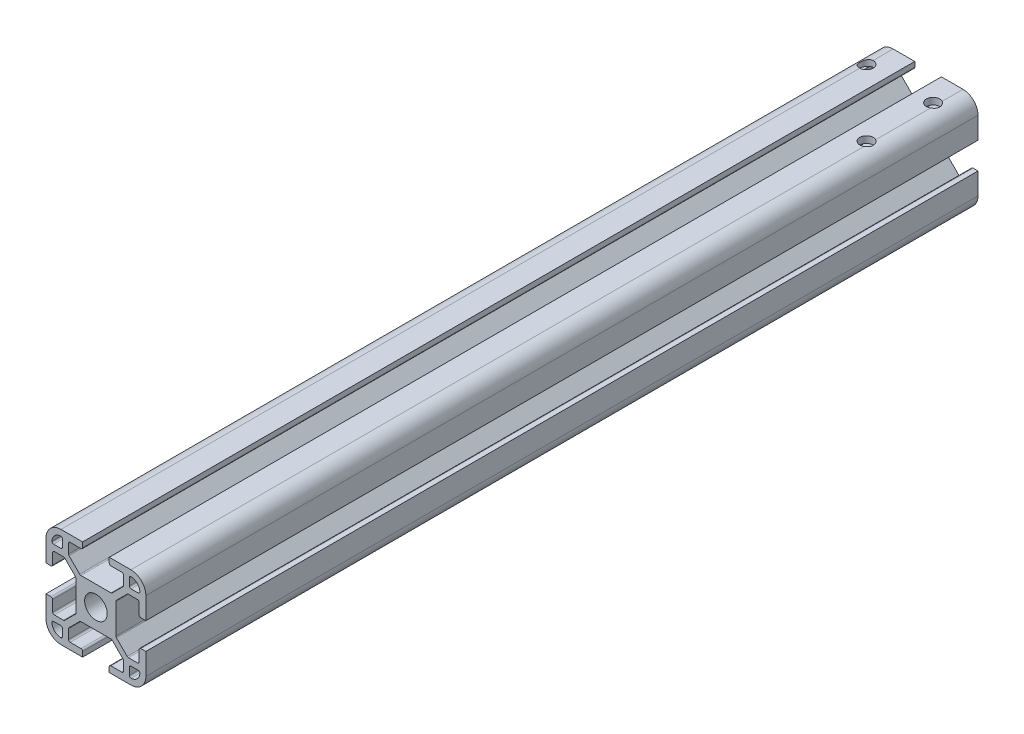
SolidWorks part; units mm, degrees
ref_plane "前基準面" through (0, 0, 0) normal (0, 0, 1) x (1, 0, 0)
ref_plane "上基準面" through (0, 0, 0) normal (0, 1, 0) x (1, 0, 0)
ref_plane "右基準面" through (0, 0, 0) normal (1, 0, 0) x (0, 0, -1)
sketch "草圖1" plane through (0, 0, 0) normal (0, 0, 1) x (1, 0, 0)
  line L0 (-15, 0) -> (0, 0) construction
  line L1 (-10.5, 15) -> (10.5, 15)
  line L2 (-15, 10.5) -> (-15, -10.5)
  line L3 (-10.5, -15) -> (10.5, -15)
  line L4 (15, 10.5) -> (15, -10.5)
  line L5 (0, 0) -> (0, 15) construction
  arc A0 (-10.5, 15) -> (-15, 10.5) centre (-10.5, 10.5) ccw
  arc A1 (-15, -10.5) -> (-10.5, -15) centre (-10.5, -10.5) ccw
  arc A2 (10.5, -15) -> (15, -10.5) centre (10.5, -10.5) ccw
  arc A3 (10.5, 15) -> (15, 10.5) centre (10.5, 10.5) cw
  circle A4 centre (0, 0) radius 3.4
  point P10 (-15, 15)
  point P17 (15, 15)
  dimension "D2" = 4.5
  dimension "D3" = 6.8
  dimension "MD1" = 30
extrude "填料-伸長1" add sketch "草圖1" against normal blind 250
sketch "草圖2" plane through (0, 0, 0) normal (0, 0, 1) x (1, 0, 0)
  line L0 (-8.25, 13) -> (-8.25, 9.5228)
  line L1 (-9.5228, 8.25) -> (-13, 8.25)
  line L2 (-8.25, 8.25) -> (-6, 6) construction
  line L3 (-9.5228, 8.25) -> (-6, 4.7272)
  line L4 (-8.25, 9.5228) -> (-4.7272, 6)
  line L5 (-7.6136, 8.8864) -> (-5.3636, 6.6364) construction
  line L6 (-8.8864, 7.6136) -> (-6.6364, 5.3636) construction
  line L7 (-8.25, 18.2) -> (-8.25, 8.25) construction
  line L8 (-8.25, 8.25) -> (-18.2, 8.25) construction
  line L9 (-4, 15) -> (-4, 13)
  line L10 (4, 15) -> (4, 13)
  line L12 (15, 4) -> (13, 4)
  line L13 (8.25, 13) -> (8.25, 9.5228)
  line L14 (9.5228, 8.25) -> (6, 4.7272)
  line L15 (8.25, 9.5228) -> (4.7272, 6)
  line L16 (-4, 13) -> (-8.25, 13)
  line L17 (4, 13) -> (8.25, 13)
  line L18 (-4, 15) -> (4, 15)
  line L19 (4.7272, 6) -> (-4.7272, 6)
  line L20 (0, 15) -> (0, 0) construction
  line L21 (10.5, 15) -> (-10.5, 15) construction
  line L22 (0, 0) -> (-15, 0) construction
  line L23 (-15, 10.5) -> (-15, -10.5) construction
  line L24 (13.2, -10.5) -> (13.2, 10.5)
  line L25 (-10.5, -13.2) -> (10.5, -13.2)
  line L26 (-13.2, 10.5) -> (-13.2, -10.5)
  line L27 (10.5, 13.2) -> (-10.5, 13.2)
  line L28 (13.2, -10.5) -> (13.2, 10.5) construction
  line L29 (-10.5, -13.2) -> (10.5, -13.2) construction
  line L30 (-13.2, 10.5) -> (-13.2, -10.5) construction
  line L31 (10.5, 13.2) -> (-10.5, 13.2) construction
  line L32 (-10.05, 13.2) -> (-10.05, 10.05)
  line L33 (-6, -6) -> (6, -6) construction
  line L34 (-6, -6) -> (-6, 6) construction
  line L35 (-6, 6) -> (6, 6) construction
  line L36 (6, -6) -> (6, 6) construction
  line L37 (-6, -6) -> (6, 6) construction
  line L38 (-6, 6) -> (6, -6) construction
  line L39 (10.05, 13.2) -> (10.05, 10.05)
  line L40 (-10.05, 10.05) -> (-13.2, 10.05)
  line L41 (10.05, 10.05) -> (13.2, 10.05)
  line L42 (10.05, -10.05) -> (13.2, -10.05)
  line L43 (10.05, -13.2) -> (10.05, -10.05)
  line L44 (-10.05, -10.05) -> (-13.2, -10.05)
  line L45 (-10.05, -13.2) -> (-10.05, -10.05)
  line L46 (-10.05, 13.2) -> (-10.5, 13.2)
  line L47 (-13.2, 10.5) -> (-13.2, 10.05)
  line L48 (-13.2, -10.5) -> (-13.2, -10.05)
  line L49 (-10.05, -13.2) -> (-10.5, -13.2)
  line L50 (10.05, -13.2) -> (10.5, -13.2)
  line L51 (13.2, -10.5) -> (13.2, -10.05)
  line L52 (13.2, 10.5) -> (13.2, 10.05)
  line L53 (10.05, 13.2) -> (10.5, 13.2)
  line L54 (-15, -4) -> (-15, 4)
  line L55 (-15, 4) -> (-13, 4)
  line L56 (-13, 4) -> (-13, 8.25)
  line L57 (-15, -4) -> (-13, -4)
  line L58 (-13, -4) -> (-13, -8.25)
  line L59 (-4, -15) -> (-4, -13)
  line L60 (-4, -13) -> (-8.25, -13)
  line L61 (-8.25, -13) -> (-8.25, -9.5228)
  line L62 (-8.25, -9.5228) -> (-4.7272, -6)
  line L63 (-9.5228, -8.25) -> (-6, -4.7272)
  line L64 (-9.5228, -8.25) -> (-13, -8.25)
  line L65 (-6, 4.7272) -> (-6, -4.7272)
  line L66 (13, 4) -> (13, 8.25)
  line L67 (9.5228, 8.25) -> (13, 8.25)
  line L68 (13, -4) -> (13, -8.25)
  line L69 (4, -15) -> (4, -13)
  line L70 (4, -13) -> (8.25, -13)
  line L71 (8.25, -13) -> (8.25, -9.5228)
  line L72 (8.25, -9.5228) -> (4.7272, -6)
  line L73 (9.5228, -8.25) -> (6, -4.7272)
  line L74 (9.5228, -8.25) -> (13, -8.25)
  line L75 (15, -4) -> (13, -4)
  line L76 (15, 4) -> (15, -4)
  line L77 (4, -15) -> (-4, -15)
  line L78 (-4.7272, -6) -> (4.7272, -6)
  line L79 (6, -4.7272) -> (6, 4.7272)
  line L80 (-10.05, 10.05) -> (-18.2, 10.05) construction
  line L81 (-10.05, 18.2) -> (-10.05, 10.05) construction
  arc A0 (10.5, -13.2) -> (13.2, -10.5) centre (10.5, -10.5) ccw
  arc A1 (10.5, 13.2) -> (13.2, 10.5) centre (10.5, 10.5) cw
  arc A16 (-10.5, 13.2) -> (-13.2, 10.5) centre (-10.5, 10.5) ccw
  arc A17 (-10.5, -13.2) -> (-13.2, -10.5) centre (-10.5, -10.5) cw
  arc A20 (13.2, 10.5) -> (10.5, 13.2) centre (10.5, 10.5) ccw
  arc A21 (10.5, -13.2) -> (13.2, -10.5) centre (10.5, -10.5) ccw
  arc A22 (-13.2, -10.5) -> (-10.5, -13.2) centre (-10.5, -10.5) ccw
  arc A23 (-10.5, 13.2) -> (-13.2, 10.5) centre (-10.5, 10.5) ccw
  arc A24 (13.2, 10.5) -> (10.5, 13.2) centre (10.5, 10.5) ccw construction
  arc A25 (10.5, -13.2) -> (13.2, -10.5) centre (10.5, -10.5) ccw construction
  arc A26 (-13.2, -10.5) -> (-10.5, -13.2) centre (-10.5, -10.5) ccw construction
  arc A27 (-10.5, 13.2) -> (-13.2, 10.5) centre (-10.5, 10.5) ccw construction
  point P86 (-10.05, -13.2)
  point P89 (-13.2, -10.05)
  point P92 (-10.05, -10.05)
  point P95 (-13, -4)
  point P98 (-6, -4.7272)
  point P101 (-13, -8.25)
  point P104 (-9.5228, -8.25)
  point P107 (-4, -13)
  point P110 (-8.25, -13)
  point P113 (-8.25, -9.5228)
  point P116 (-4.7272, -6)
  point P119 (4, -13)
  point P122 (8.25, -13)
  point P125 (10.05, -13.2)
  point P128 (13.2, -10.05)
  point P131 (10.05, -10.05)
  point P134 (8.25, -9.5228)
  point P137 (4.7272, -6)
  point P140 (13, -4)
  point P143 (13, -8.25)
  point P146 (9.5228, -8.25)
  point P149 (6, -4.7272)
  point P152 (6, 4.7272)
  point P155 (13, 4)
  point P158 (13, 8.25)
  point P161 (9.5228, 8.25)
  point P164 (13.2, 10.05)
  point P167 (10.05, 10.05)
  point P170 (10.05, 13.2)
  point P173 (-6, 4.7272)
  point P176 (-4.7272, 6)
  point P179 (4.7272, 6)
  point P182 (8.25, 9.5228)
  point P185 (8.25, 13)
  point P188 (4, 13)
  point P191 (-4, 13)
  point P194 (-8.25, 13)
  point P197 (-9.5228, 8.25)
  point P200 (-13, 4)
  point P203 (-13, 8.25)
  point P207 (-13.2, 10.05)
  dimension "D2" = 12
  dimension "MD8" = 8
  dimension "D9" = 7
  dimension "MD3" = 16.5
  dimension "MD4" = 16.5
  dimension "D1" = 1.8
  dimension "D5" = 1.8
  dimension "D6" = 0.9
  dimension "D7" = 0.9
extrude "除料-伸長1" cut sketch "草圖2" against normal up to next
fillet "圓角1" radius 0.5 44 edges at (-4, -13, -125) (4, -13, -125) (4, 13, -125) (9.5228, 8.25, -125) (13, 8.25, -125) (13, 4, -125) (13, -4, -125) (9.5228, -8.25, -125) (13, -8.25, -125) (8.25, -13, -125) (-8.25, -13, -125) (8.25, -9.5228, -125) (-8.25, -9.5228, -125) (-4.7272, -6, -125) (4.7272, -6, -125) (6, -4.7272, -125) (6, 4.7272, -125) (4.7272, 6, -125) (-6, 4.7272, -125) (-6, -4.7272, -125) (-9.5228, -8.25, -125) (-13, -8.25, -125) (-13, -4, -125) (-13, 4, -125) (-9.5228, 8.25, -125) (-13, 8.25, -125) (-4.7272, 6, -125) (-8.25, 9.5228, -125) (-4, 13, -125) (-8.25, 13, -125) (10.05, 13.2, -125) (10.05, 10.05, -125) (13.2, 10.05, -125) (-10.05, 13.2, -125) (-10.05, 10.05, -125) (-13.2, 10.05, -125) (-13.2, -10.05, -125) (-10.05, -13.2, -125) (10.05, -13.2, -125) (13.2, -10.05, -125) (10.05, -10.05, -125) (-10.05, -10.05, -125) (8.25, 9.5228, -125) (8.25, 13, -125)
sketch "草圖3" plane through (0, 0, 0) normal (0, 0, 1) x (1, 0, 0)
  line L0 (0, 21.6264) -> (0, 0) construction
  line L1 (-3.4, 0) -> (3.4, 0)
  line L2 (3.9, 0.5) -> (3.9, 0.8)
  line L3 (3.9, 0.8) -> (6.7235, 0.8)
  line L4 (7.1787, 1.5069) -> (5.1332, 6.0069)
  line L5 (4.678, 6.3) -> (-4.678, 6.3)
  line L6 (-7.1787, 1.5069) -> (-5.1332, 6.0069)
  line L7 (-3.9, 0.8) -> (-6.7235, 0.8)
  line L8 (-3.9, 0.5) -> (-3.9, 0.8)
  arc A0 (3.4, 0) -> (3.9, 0.5) centre (3.4, 0.5) ccw
  arc A1 (-3.9, 0.5) -> (-3.4, 0) centre (-3.4, 0.5) ccw
  arc A2 (-7.1787, 1.5069) -> (-6.7235, 0.8) centre (-6.7235, 1.3) ccw
  arc A3 (-5.1332, 6.0069) -> (-4.678, 6.3) centre (-4.678, 5.8) cw
  arc A4 (5.1332, 6.0069) -> (4.678, 6.3) centre (4.678, 5.8) ccw
  arc A5 (6.7235, 0.8) -> (7.1787, 1.5069) centre (6.7235, 1.3) ccw
  point P9 (0, 6.3)
  point P14 (3.9, 0)
  point P17 (-3.9, 0)
  point P20 (-7.5, 0.8)
  point P23 (-5, 6.3)
  point P26 (5, 6.3)
  point P29 (7.5, 0.8)
  dimension "D6" = 0.5
  dimension "D1" = 7.8
  dimension "D2" = 15
  dimension "D3" = 5.5
  dimension "D4" = 6.3
  dimension "D5" = 10
extrude "填料-伸長2" [suppressed] add sketch "草圖3" along normal mid plane 14
hole_wizard "M4 螺紋孔1" [suppressed] positions "草圖6" profile "草圖7" tap size "M4" standard "ISO"
sketch "草圖6" [suppressed] plane through (0.7411, 0, -5.4586) normal (0, 1, 0) x (-1, 0, 0)
  point P0 (0.7411, 5.4586)
sketch "草圖7" plane through (0, 0, 0) normal (1, 0, 0) x (0, 0, -1)
  line L0 (0, 0) -> (0, 6.3)
  line L1 (0, 6.3) -> (1.65, 6.3)
  line L2 (1.65, 6.3) -> (1.65, 0)
  line L5 (1.65, 0) -> (0, 0)
  line L11 (0, -6.35) -> (0, 107.95) construction
  dimension "貫穿螺孔鑽直徑" = 3.3
  dimension "貫穿螺孔鑽深度" = 6.3
cosmetic thread "鑽孔螺紋2" parameters "D2"=4
sketch "草圖8" plane through (0, 0, 0) normal (0, 0, 1) x (1, 0, 0)
  line L0 (-4, 30) -> (-30, 4)
  line L1 (0, 0) -> (-30, 0)
  line L2 (0, 0) -> (0, 30)
  line L3 (0, 30) -> (-4, 30)
  line L4 (-30, 0) -> (-30, 4)
  line L7 (-30, 4) -> (-4, 4) construction
  line L8 (-4, 30) -> (-4, 4) construction
  dimension "D1" = 30
  dimension "D2" = 30
  dimension "D3" = 4
  dimension "D4" = 4
extrude "填料-伸長3" [suppressed] add sketch "草圖8" along normal mid plane 20
shell "薄殼1" [suppressed] thickness 4
hole_wizard "M4 螺紋孔2" [suppressed] positions "草圖11" profile "草圖12" tap size "M4" standard "ISO"
sketch "草圖11" [suppressed] plane through (0, 4, 0) normal (0, 1, 0) x (-1, 0, 0)
  line L0 (17, 6) -> (17, 0) construction
  line L1 (30, 6) -> (4, 6) construction
  line L2 (17, 0) -> (30, 0) construction
  line L3 (30, 6) -> (30, -6) construction
  point P0 (17, 0)
sketch "草圖12" plane through (-17, 4, 0) normal (1, 0, 0) x (0, 0, 1)
  line L0 (0, 0) -> (0, 19)
  line L1 (0, 19) -> (1.65, 19)
  line L2 (1.65, 19) -> (1.65, 0)
  line L5 (1.65, 0) -> (0, 0)
  line L11 (0, -6.35) -> (0, 107.95) construction
  dimension "貫穿螺孔鑽直徑" = 3.3
  dimension "貫穿螺孔鑽深度" = 19
cosmetic thread "鑽孔螺紋3" parameters "D2"=4
hole_wizard "M4 螺紋孔3" [suppressed] positions "草圖13" profile "草圖14" tap size "M4" standard "ISO"
sketch "草圖13" [suppressed] plane through (-4, 0, 0) normal (-1, 0, 0) x (0, -1, 0)
  line L0 (-17, 6) -> (-17, 0) construction
  line L2 (-17, 0) -> (-4, 0) construction
  line L4 (-4, 6) -> (-30, 6) construction
  line L5 (-4, 6) -> (-4, -6) construction
  point P0 (-17, 0)
sketch "草圖14" plane through (-4, 17, 0) normal (0, 1, 0) x (0, 0, 1)
  line L0 (0, 0) -> (0, 19)
  line L1 (0, 19) -> (1.65, 19)
  line L2 (1.65, 19) -> (1.65, 0)
  line L5 (1.65, 0) -> (0, 0)
  line L11 (0, -6.35) -> (0, 107.95) construction
  dimension "貫穿螺孔鑽直徑" = 3.3
  dimension "貫穿螺孔鑽深度" = 4
cosmetic thread "鑽孔螺紋3" parameters "D2"=4
fillet "圓角2" [suppressed] radius 1
fillet "圓角3" [suppressed] radius 1
sketch "草圖15" plane through (0, 15, 0) normal (0, 1, 0) x (1, 0, 0)
  line L0 (9.5, 255.2187) -> (9.5, 209.2615) construction
  line L1 (10.5, 250) -> (4, 250) construction
  line L2 (15, 250) -> (15, 0) construction
  line L3 (9.5, 242) -> (-25.8607, 242) construction
  circle A0 centre (9.5, 242) radius 2
  circle A1 centre (9.5, 222) radius 2
  circle A2 centre (-10.5, 242) radius 2
  dimension "D1" = 4
  dimension "D2" = 4
  dimension "D6" = 4
  dimension "D3" = 20
  dimension "D4" = 8
  dimension "D5" = 5.5
  dimension "D7" = 20
extrude "除料-伸長2" cut sketch "草圖15" against normal up to surface (2 mm away) up to face at (6.125, 13, -125)
